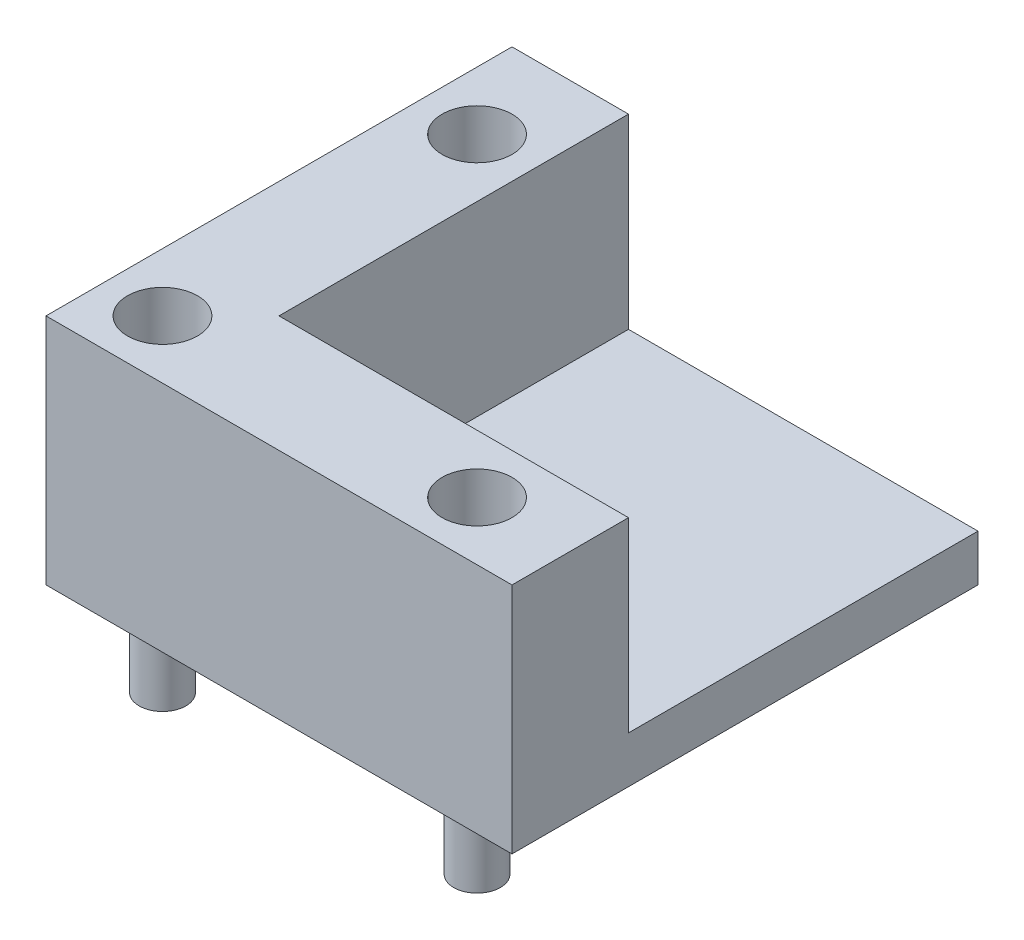
SolidWorks part; units mm, degrees
ref_plane "Front Plane" through (0, 0, 0) normal (0, 0, 1) x (1, 0, 0)
ref_plane "Top Plane" through (0, 0, 0) normal (0, 1, 0) x (1, 0, 0)
ref_plane "Right Plane" through (0, 0, 0) normal (1, 0, 0) x (0, 0, -1)
sketch "Sketch1" plane through (0, 0, 0) normal (0, 1, 0) x (1, 0, 0)
  line L1 (0, 0) -> (25.4, 0)
  line L2 (0, 0) -> (0, 25.4)
  line L3 (0, 25.4) -> (25.4, 25.4)
  line L4 (25.4, 0) -> (25.4, 25.4)
  dimension "D1" = 25.4
  dimension "D2" = 25.4
extrude "Boss-Extrude1" add sketch "Sketch1" along normal blind 2.54
sketch "Sketch2" plane through (0, 2.54, 0) normal (0, 1, 0) x (1, 0, 0)
  line L0 (0, 25.4) -> (0, 0)
  line L1 (0, 0) -> (25.4, 0)
  line L2 (25.4, 0) -> (25.4, 6.35)
  line L3 (25.4, 0) -> (25.4, 25.4) construction
  line L4 (0, 25.4) -> (6.35, 25.4)
  line L5 (25.4, 25.4) -> (0, 25.4) construction
  line L6 (6.35, 25.4) -> (6.35, 6.35)
  line L7 (6.35, 6.35) -> (25.4, 6.35)
  dimension "D1" = 6.35
  dimension "D2" = 6.35
extrude "Boss-Extrude2" add sketch "Sketch2" along normal blind 10.16
sketch "Sketch3" plane through (0, 12.7, 0) normal (0, 1, 0) x (1, 0, 0)
  line L0 (3.175, 25.4) -> (3.175, 0) construction
  line L1 (6.35, 25.4) -> (0, 25.4) construction
  line L2 (0, 0) -> (25.4, 0) construction
  line L3 (25.4, 3.175) -> (3.175, 3.175) construction
  line L4 (25.4, 0) -> (25.4, 6.35) construction
  circle A0 centre (3.175, 20.32) radius 1.905
  circle A1 centre (3.175, 3.175) radius 1.905
  circle A2 centre (20.32, 3.175) radius 1.905
  dimension "D1" = 3.81
  dimension "D2" = 5.08
  dimension "D3" = 3.81
  dimension "D4" = 3.81
  dimension "D5" = 5.08
extrude "Cut-Extrude1" cut sketch "Sketch3" against normal blind 6.35
sketch "Sketch4" plane through (0, 0, 0) normal (0, -1, 0) x (1, 0, 0)
  line L0 (25.4, -3.175) -> (0, -3.175) construction
  line L1 (25.4, 0) -> (25.4, -25.4) construction
  line L2 (0, -25.4) -> (0, 0) construction
  line L3 (3.175, 0) -> (3.175, -25.4) construction
  line L4 (0, 0) -> (25.4, 0) construction
  line L5 (25.4, -25.4) -> (0, -25.4) construction
  circle A0 centre (3.175, -3.175) radius 1.27
  circle A1 centre (20.32, -3.175) radius 1.27
  circle A2 centre (3.175, -20.32) radius 1.27
  dimension "D3" = 2.54
  dimension "D4" = 2.54
  dimension "D5" = 2.54
  dimension "D6" = 5.08
  dimension "D7" = 5.08
  dimension "D8" = 3.175
  dimension "D1" = 3.175
  dimension "D2" = 3.175
extrude "Boss-Extrude3" add sketch "Sketch4" along normal blind 5.08
